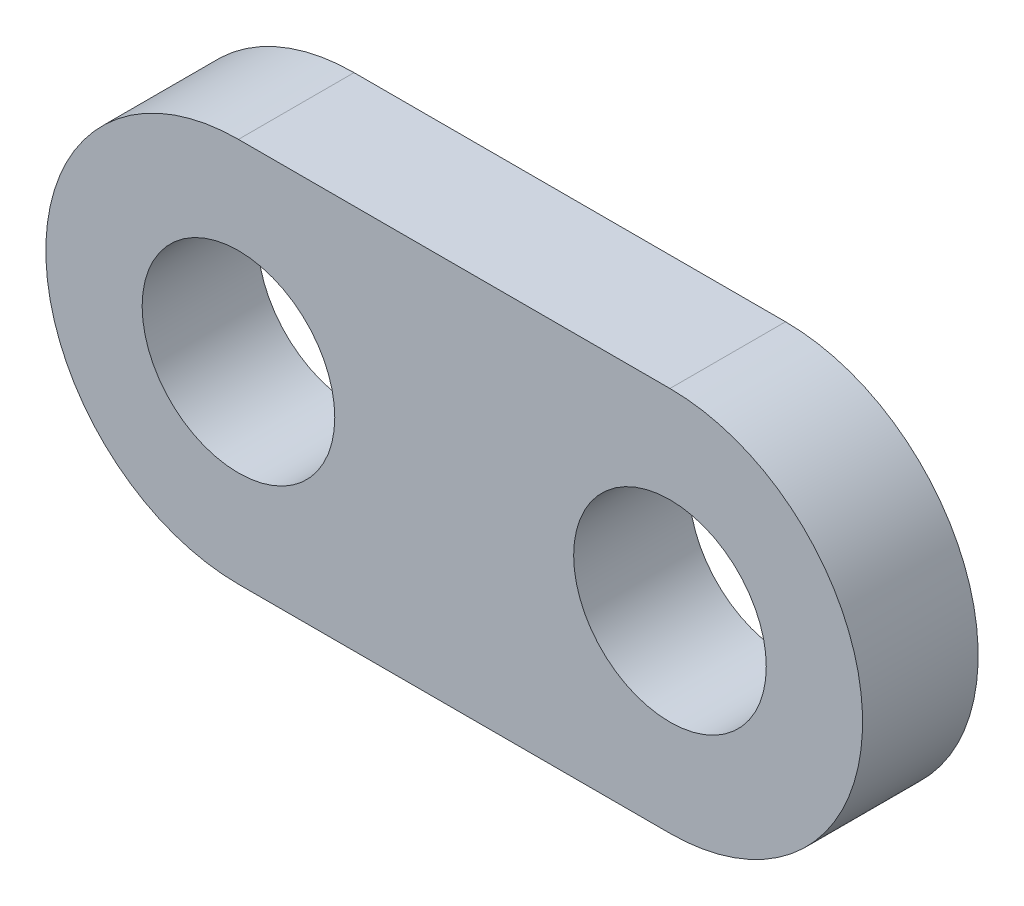
SolidWorks part; units mm, degrees
ref_plane "Alzado" through (0, 0, 0) normal (0, 0, 1) x (1, 0, 0)
ref_plane "Planta" through (0, 0, 0) normal (0, 1, 0) x (1, 0, 0)
ref_plane "Vista lateral" through (0, 0, 0) normal (1, 0, 0) x (0, 0, -1)
sketch "Croquis1" plane through (0, 0, 0) normal (0, 0, 1) x (1, 0, 0)
  line L0 (-11.2242, 0) -> (11.1758, 0) construction
  line L1 (-11.2242, 10) -> (11.1758, 10)
  line L2 (-11.2242, -10) -> (11.1758, -10)
  arc A0 (-11.2242, 10) -> (-11.2242, -10) centre (-11.2242, 0) ccw
  arc A1 (11.1758, -10) -> (11.1758, 10) centre (11.1758, 0) ccw
  circle A2 centre (-11.2242, 0) radius 5
  circle A3 centre (11.1758, 0) radius 5
  point P3 (-0.0242, 0)
  dimension "D2" = 10
  dimension "D3" = 10
  dimension "D1" = 22.4
extrude "Saliente-Extruir1" add sketch "Croquis1" along normal blind 6
